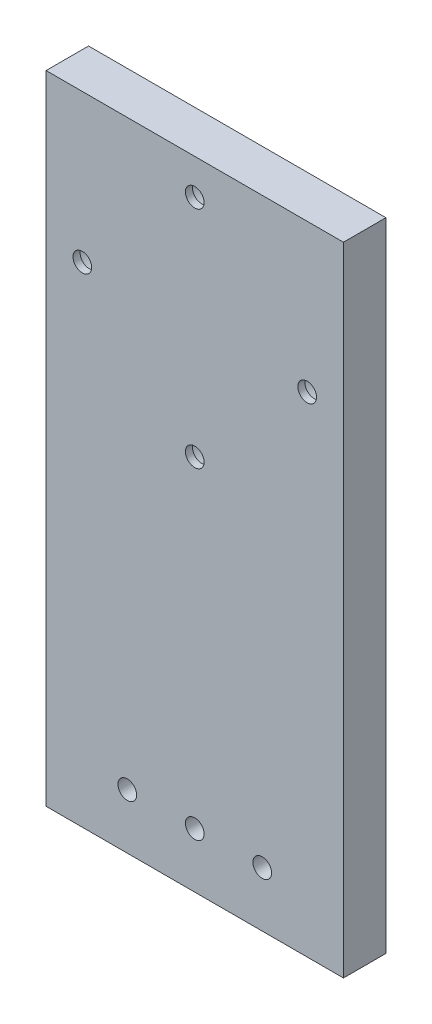
SolidWorks part; units mm, degrees
ref_plane "Front Plane" through (0, 0, 0) normal (0, 0, 1) x (1, 0, 0)
ref_plane "Top Plane" through (0, 0, 0) normal (0, 1, 0) x (1, 0, 0)
ref_plane "Right Plane" through (0, 0, 0) normal (1, 0, 0) x (0, 0, -1)
sketch "Sketch1" plane through (0, 0, 0) normal (0, 0, 1) x (1, 0, 0)
  line L0 (0, 0) -> (50000, 0) construction
  line L1 (0, 0) -> (0, -50000) construction
  line L2 (-9.53, -61.35) -> (49990.47, -61.35) construction
  line L3 (0, 20.875) -> (0, 25.2632) construction
  line L4 (-21, 20.875) -> (21, 20.875)
  line L5 (-21, 20.875) -> (-21, -69.125)
  line L6 (-21, -69.125) -> (21, -69.125)
  line L7 (21, 20.875) -> (21, -69.125)
  line L13 (0, 9.53) -> (0, -4.4139) construction
  circle A0 centre (0, 0) radius 20 construction
  circle A1 centre (0, -15.875) radius 1.32
  circle A2 centre (-15.875, 0) radius 1.32
  circle A3 centre (0, 15.875) radius 1.32
  circle A4 centre (-9.53, -61.35) radius 1.32
  circle A5 centre (0, -61.35) radius 1.32
  circle A6 centre (9.53, -61.35) radius 1.32
  circle A7 centre (15.875, 0) radius 1.32
  point P19 (0, 0)
  point P24 (0, 0)
  dimension "D3" = 2.64
  dimension "D8" = 61.35
  dimension "D9" = 9.53
  dimension "D10" = 42
  dimension "D13" = 5.125
  dimension "D11" = 90
  dimension "D2" = 40
  dimension "D6" = 15.875
  dimension "D7" = 3
  dimension "D5" = 4
  dimension "D1" = 2.64
  dimension "D12" = 5
  dimension "D4" = 15.875
extrude "Boss-Extrude1" add sketch "Sketch1" along normal blind 6
sketch "Sketch2" plane through (0, 0, 0) normal (0, 0, -1) x (-1, 0, 0)
  circle A0 centre (-15.875, 0) radius 3.25
  circle A1 centre (0, 15.875) radius 3.25
  circle A2 centre (15.875, 0) radius 3.25
  circle A3 centre (0, -15.875) radius 3.25
  circle A5 centre (-15.875, 0) radius 1.32 construction
  circle A6 centre (0, 15.875) radius 1.32 construction
  point P12 (0, 0)
  dimension "D1" = 6.5
  dimension "D2" = 4
extrude "Cut-Extrude1" cut sketch "Sketch2" against normal blind 5
sketch "Sketch3" plane through (0, 0, 6) normal (0, 0, 1) x (1, 0, 0)
  circle A0 centre (0, 0) radius 15.875 construction
sketch "Sketch4" plane through (0, 0, 0) normal (0, 1, 0) x (1, 0, 0)
  line L0 (0, 0) -> (0, -18.0356) construction
equation "\"A\"=61.35"
equation "\"D8@Sketch1\"=\"A\""
